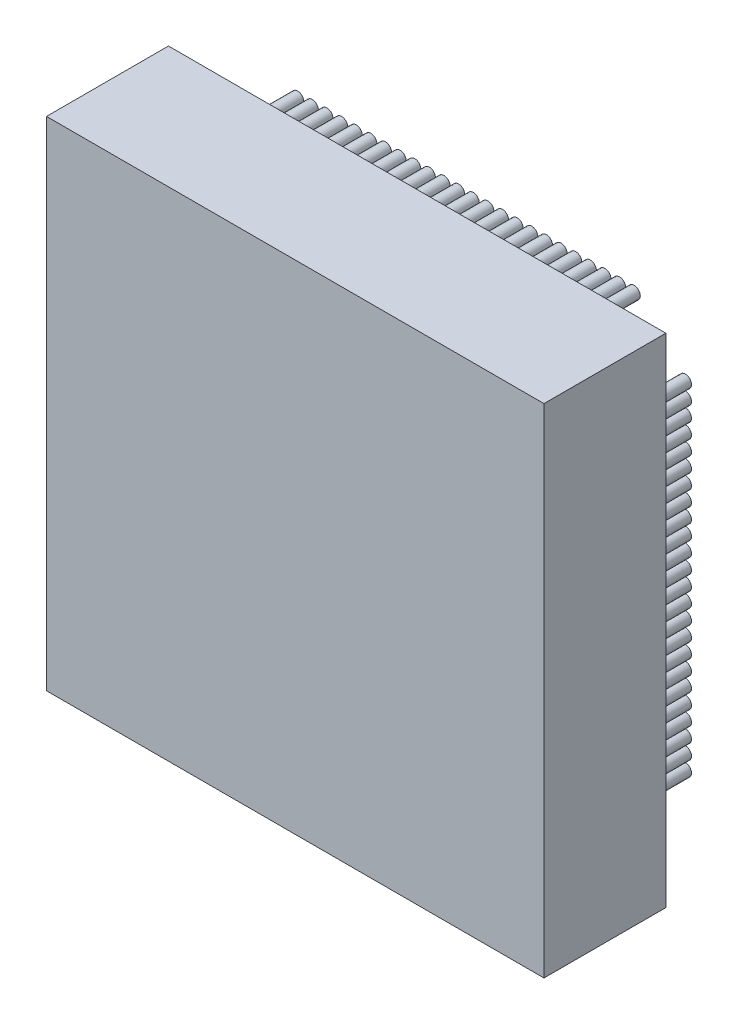
SolidWorks part; units mm, degrees
ref_plane "Front Plane" through (0, 0, 0) normal (0, 0, 1) x (1, 0, 0)
ref_plane "Top Plane" through (0, 0, 0) normal (0, 1, 0) x (1, 0, 0)
ref_plane "Right Plane" through (0, 0, 0) normal (1, 0, 0) x (0, 0, -1)
sketch "Sketch1" plane through (0, 0, 0) normal (0, 0, 1) x (1, 0, 0)
  line L0 (10.2, -10.2) -> (10.2, 10.2)
  line L1 (10.2, 10.2) -> (-10.2, 10.2)
  line L2 (-10.2, 10.2) -> (-10.2, -10.2)
  line L3 (-10.2, -10.2) -> (10.2, -10.2)
extrude "Component_Outline" add sketch "Sketch1" along normal blind 5 separate body
sketch "Sketch2" plane through (0, 0, 0) normal (0, 0, 1) x (1, 0, 0)
  circle A0 centre (-6.9, -9) radius 0.25
extrude "1" add sketch "Sketch2" against normal blind 2 separate body
sketch "Sketch3" plane through (0, 0, 0) normal (0, 0, 1) x (1, 0, 0)
  circle A0 centre (-6.3, -9) radius 0.25
extrude "2" add sketch "Sketch3" against normal blind 2 separate body
sketch "Sketch4" plane through (0, 0, 0) normal (0, 0, 1) x (1, 0, 0)
  circle A0 centre (-5.7, -9) radius 0.25
extrude "3" add sketch "Sketch4" against normal blind 2 separate body
sketch "Sketch5" plane through (0, 0, 0) normal (0, 0, 1) x (1, 0, 0)
  circle A0 centre (-5.1, -9) radius 0.25
extrude "4" add sketch "Sketch5" against normal blind 2 separate body
sketch "Sketch6" plane through (0, 0, 0) normal (0, 0, 1) x (1, 0, 0)
  circle A0 centre (-4.5, -9) radius 0.25
extrude "5" add sketch "Sketch6" against normal blind 2 separate body
sketch "Sketch7" plane through (0, 0, 0) normal (0, 0, 1) x (1, 0, 0)
  circle A0 centre (-3.9, -9) radius 0.25
extrude "6" add sketch "Sketch7" against normal blind 2 separate body
sketch "Sketch8" plane through (0, 0, 0) normal (0, 0, 1) x (1, 0, 0)
  circle A0 centre (-3.3, -9) radius 0.25
extrude "7" add sketch "Sketch8" against normal blind 2 separate body
sketch "Sketch9" plane through (0, 0, 0) normal (0, 0, 1) x (1, 0, 0)
  circle A0 centre (-2.7, -9) radius 0.25
extrude "8" add sketch "Sketch9" against normal blind 2 separate body
sketch "Sketch10" plane through (0, 0, 0) normal (0, 0, 1) x (1, 0, 0)
  circle A0 centre (-2.1, -9) radius 0.25
extrude "9" add sketch "Sketch10" against normal blind 2 separate body
sketch "Sketch11" plane through (0, 0, 0) normal (0, 0, 1) x (1, 0, 0)
  circle A0 centre (-1.5, -9) radius 0.25
extrude "10" add sketch "Sketch11" against normal blind 2 separate body
sketch "Sketch12" plane through (0, 0, 0) normal (0, 0, 1) x (1, 0, 0)
  circle A0 centre (-0.9, -9) radius 0.25
extrude "11" add sketch "Sketch12" against normal blind 2 separate body
sketch "Sketch13" plane through (0, 0, 0) normal (0, 0, 1) x (1, 0, 0)
  circle A0 centre (-0.3, -9) radius 0.25
extrude "12" add sketch "Sketch13" against normal blind 2 separate body
sketch "Sketch14" plane through (0, 0, 0) normal (0, 0, 1) x (1, 0, 0)
  circle A0 centre (0.3, -9) radius 0.25
extrude "13" add sketch "Sketch14" against normal blind 2 separate body
sketch "Sketch15" plane through (0, 0, 0) normal (0, 0, 1) x (1, 0, 0)
  circle A0 centre (0.9, -9) radius 0.25
extrude "14" add sketch "Sketch15" against normal blind 2 separate body
sketch "Sketch16" plane through (0, 0, 0) normal (0, 0, 1) x (1, 0, 0)
  circle A0 centre (1.5, -9) radius 0.25
extrude "15" add sketch "Sketch16" against normal blind 2 separate body
sketch "Sketch17" plane through (0, 0, 0) normal (0, 0, 1) x (1, 0, 0)
  circle A0 centre (2.1, -9) radius 0.25
extrude "16" add sketch "Sketch17" against normal blind 2 separate body
sketch "Sketch18" plane through (0, 0, 0) normal (0, 0, 1) x (1, 0, 0)
  circle A0 centre (2.7, -9) radius 0.25
extrude "17" add sketch "Sketch18" against normal blind 2 separate body
sketch "Sketch19" plane through (0, 0, 0) normal (0, 0, 1) x (1, 0, 0)
  circle A0 centre (3.3, -9) radius 0.25
extrude "18" add sketch "Sketch19" against normal blind 2 separate body
sketch "Sketch20" plane through (0, 0, 0) normal (0, 0, 1) x (1, 0, 0)
  circle A0 centre (3.9, -9) radius 0.25
extrude "19" add sketch "Sketch20" against normal blind 2 separate body
sketch "Sketch21" plane through (0, 0, 0) normal (0, 0, 1) x (1, 0, 0)
  circle A0 centre (4.5, -9) radius 0.25
extrude "20" add sketch "Sketch21" against normal blind 2 separate body
sketch "Sketch22" plane through (0, 0, 0) normal (0, 0, 1) x (1, 0, 0)
  circle A0 centre (5.1, -9) radius 0.25
extrude "21" add sketch "Sketch22" against normal blind 2 separate body
sketch "Sketch23" plane through (0, 0, 0) normal (0, 0, 1) x (1, 0, 0)
  circle A0 centre (5.7, -9) radius 0.25
extrude "22" add sketch "Sketch23" against normal blind 2 separate body
sketch "Sketch24" plane through (0, 0, 0) normal (0, 0, 1) x (1, 0, 0)
  circle A0 centre (6.3, -9) radius 0.25
extrude "23" add sketch "Sketch24" against normal blind 2 separate body
sketch "Sketch25" plane through (0, 0, 0) normal (0, 0, 1) x (1, 0, 0)
  circle A0 centre (6.9, -9) radius 0.25
extrude "24" add sketch "Sketch25" against normal blind 2 separate body
sketch "Sketch26" plane through (0, 0, 0) normal (0, 0, 1) x (1, 0, 0)
  circle A0 centre (9, -6.9) radius 0.25
extrude "25" add sketch "Sketch26" against normal blind 2 separate body
sketch "Sketch27" plane through (0, 0, 0) normal (0, 0, 1) x (1, 0, 0)
  circle A0 centre (9, -6.3) radius 0.25
extrude "26" add sketch "Sketch27" against normal blind 2 separate body
sketch "Sketch28" plane through (0, 0, 0) normal (0, 0, 1) x (1, 0, 0)
  circle A0 centre (9, -5.7) radius 0.25
extrude "27" add sketch "Sketch28" against normal blind 2 separate body
sketch "Sketch29" plane through (0, 0, 0) normal (0, 0, 1) x (1, 0, 0)
  circle A0 centre (9, -5.1) radius 0.25
extrude "28" add sketch "Sketch29" against normal blind 2 separate body
sketch "Sketch30" plane through (0, 0, 0) normal (0, 0, 1) x (1, 0, 0)
  circle A0 centre (9, -4.5) radius 0.25
extrude "29" add sketch "Sketch30" against normal blind 2 separate body
sketch "Sketch31" plane through (0, 0, 0) normal (0, 0, 1) x (1, 0, 0)
  circle A0 centre (9, -3.9) radius 0.25
extrude "30" add sketch "Sketch31" against normal blind 2 separate body
sketch "Sketch32" plane through (0, 0, 0) normal (0, 0, 1) x (1, 0, 0)
  circle A0 centre (9, -3.3) radius 0.25
extrude "31" add sketch "Sketch32" against normal blind 2 separate body
sketch "Sketch33" plane through (0, 0, 0) normal (0, 0, 1) x (1, 0, 0)
  circle A0 centre (9, -2.7) radius 0.25
extrude "32" add sketch "Sketch33" against normal blind 2 separate body
sketch "Sketch34" plane through (0, 0, 0) normal (0, 0, 1) x (1, 0, 0)
  circle A0 centre (9, -2.1) radius 0.25
extrude "33" add sketch "Sketch34" against normal blind 2 separate body
sketch "Sketch35" plane through (0, 0, 0) normal (0, 0, 1) x (1, 0, 0)
  circle A0 centre (9, -1.5) radius 0.25
extrude "34" add sketch "Sketch35" against normal blind 2 separate body
sketch "Sketch36" plane through (0, 0, 0) normal (0, 0, 1) x (1, 0, 0)
  circle A0 centre (9, -0.9) radius 0.25
extrude "35" add sketch "Sketch36" against normal blind 2 separate body
sketch "Sketch37" plane through (0, 0, 0) normal (0, 0, 1) x (1, 0, 0)
  circle A0 centre (9, -0.3) radius 0.25
extrude "36" add sketch "Sketch37" against normal blind 2 separate body
sketch "Sketch38" plane through (0, 0, 0) normal (0, 0, 1) x (1, 0, 0)
  circle A0 centre (9, 0.3) radius 0.25
extrude "37" add sketch "Sketch38" against normal blind 2 separate body
sketch "Sketch39" plane through (0, 0, 0) normal (0, 0, 1) x (1, 0, 0)
  circle A0 centre (9, 0.9) radius 0.25
extrude "38" add sketch "Sketch39" against normal blind 2 separate body
sketch "Sketch40" plane through (0, 0, 0) normal (0, 0, 1) x (1, 0, 0)
  circle A0 centre (9, 1.5) radius 0.25
extrude "39" add sketch "Sketch40" against normal blind 2 separate body
sketch "Sketch41" plane through (0, 0, 0) normal (0, 0, 1) x (1, 0, 0)
  circle A0 centre (9, 2.1) radius 0.25
extrude "40" add sketch "Sketch41" against normal blind 2 separate body
sketch "Sketch42" plane through (0, 0, 0) normal (0, 0, 1) x (1, 0, 0)
  circle A0 centre (9, 2.7) radius 0.25
extrude "41" add sketch "Sketch42" against normal blind 2 separate body
sketch "Sketch43" plane through (0, 0, 0) normal (0, 0, 1) x (1, 0, 0)
  circle A0 centre (9, 3.3) radius 0.25
extrude "42" add sketch "Sketch43" against normal blind 2 separate body
sketch "Sketch44" plane through (0, 0, 0) normal (0, 0, 1) x (1, 0, 0)
  circle A0 centre (9, 3.9) radius 0.25
extrude "43" add sketch "Sketch44" against normal blind 2 separate body
sketch "Sketch45" plane through (0, 0, 0) normal (0, 0, 1) x (1, 0, 0)
  circle A0 centre (9, 4.5) radius 0.25
extrude "44" add sketch "Sketch45" against normal blind 2 separate body
sketch "Sketch46" plane through (0, 0, 0) normal (0, 0, 1) x (1, 0, 0)
  circle A0 centre (9, 5.1) radius 0.25
extrude "45" add sketch "Sketch46" against normal blind 2 separate body
sketch "Sketch47" plane through (0, 0, 0) normal (0, 0, 1) x (1, 0, 0)
  circle A0 centre (9, 5.7) radius 0.25
extrude "46" add sketch "Sketch47" against normal blind 2 separate body
sketch "Sketch48" plane through (0, 0, 0) normal (0, 0, 1) x (1, 0, 0)
  circle A0 centre (9, 6.3) radius 0.25
extrude "47" add sketch "Sketch48" against normal blind 2 separate body
sketch "Sketch49" plane through (0, 0, 0) normal (0, 0, 1) x (1, 0, 0)
  circle A0 centre (9, 6.9) radius 0.25
extrude "48" add sketch "Sketch49" against normal blind 2 separate body
sketch "Sketch50" plane through (0, 0, 0) normal (0, 0, 1) x (1, 0, 0)
  circle A0 centre (6.9, 9) radius 0.25
extrude "49" add sketch "Sketch50" against normal blind 2 separate body
sketch "Sketch51" plane through (0, 0, 0) normal (0, 0, 1) x (1, 0, 0)
  circle A0 centre (6.3, 9) radius 0.25
extrude "50" add sketch "Sketch51" against normal blind 2 separate body
sketch "Sketch52" plane through (0, 0, 0) normal (0, 0, 1) x (1, 0, 0)
  circle A0 centre (5.7, 9) radius 0.25
extrude "51" add sketch "Sketch52" against normal blind 2 separate body
sketch "Sketch53" plane through (0, 0, 0) normal (0, 0, 1) x (1, 0, 0)
  circle A0 centre (5.1, 9) radius 0.25
extrude "52" add sketch "Sketch53" against normal blind 2 separate body
sketch "Sketch54" plane through (0, 0, 0) normal (0, 0, 1) x (1, 0, 0)
  circle A0 centre (4.5, 9) radius 0.25
extrude "53" add sketch "Sketch54" against normal blind 2 separate body
sketch "Sketch55" plane through (0, 0, 0) normal (0, 0, 1) x (1, 0, 0)
  circle A0 centre (3.9, 9) radius 0.25
extrude "54" add sketch "Sketch55" against normal blind 2 separate body
sketch "Sketch56" plane through (0, 0, 0) normal (0, 0, 1) x (1, 0, 0)
  circle A0 centre (3.3, 9) radius 0.25
extrude "55" add sketch "Sketch56" against normal blind 2 separate body
sketch "Sketch57" plane through (0, 0, 0) normal (0, 0, 1) x (1, 0, 0)
  circle A0 centre (2.7, 9) radius 0.25
extrude "56" add sketch "Sketch57" against normal blind 2 separate body
sketch "Sketch58" plane through (0, 0, 0) normal (0, 0, 1) x (1, 0, 0)
  circle A0 centre (2.1, 9) radius 0.25
extrude "57" add sketch "Sketch58" against normal blind 2 separate body
sketch "Sketch59" plane through (0, 0, 0) normal (0, 0, 1) x (1, 0, 0)
  circle A0 centre (1.5, 9) radius 0.25
extrude "58" add sketch "Sketch59" against normal blind 2 separate body
sketch "Sketch60" plane through (0, 0, 0) normal (0, 0, 1) x (1, 0, 0)
  circle A0 centre (0.9, 9) radius 0.25
extrude "59" add sketch "Sketch60" against normal blind 2 separate body
sketch "Sketch61" plane through (0, 0, 0) normal (0, 0, 1) x (1, 0, 0)
  circle A0 centre (0.3, 9) radius 0.25
extrude "60" add sketch "Sketch61" against normal blind 2 separate body
sketch "Sketch62" plane through (0, 0, 0) normal (0, 0, 1) x (1, 0, 0)
  circle A0 centre (-0.3, 9) radius 0.25
extrude "61" add sketch "Sketch62" against normal blind 2 separate body
sketch "Sketch63" plane through (0, 0, 0) normal (0, 0, 1) x (1, 0, 0)
  circle A0 centre (-0.9, 9) radius 0.25
extrude "62" add sketch "Sketch63" against normal blind 2 separate body
sketch "Sketch64" plane through (0, 0, 0) normal (0, 0, 1) x (1, 0, 0)
  circle A0 centre (-1.5, 9) radius 0.25
extrude "63" add sketch "Sketch64" against normal blind 2 separate body
sketch "Sketch65" plane through (0, 0, 0) normal (0, 0, 1) x (1, 0, 0)
  circle A0 centre (-2.1, 9) radius 0.25
extrude "64" add sketch "Sketch65" against normal blind 2 separate body
sketch "Sketch66" plane through (0, 0, 0) normal (0, 0, 1) x (1, 0, 0)
  circle A0 centre (-2.7, 9) radius 0.25
extrude "65" add sketch "Sketch66" against normal blind 2 separate body
sketch "Sketch67" plane through (0, 0, 0) normal (0, 0, 1) x (1, 0, 0)
  circle A0 centre (-3.3, 9) radius 0.25
extrude "66" add sketch "Sketch67" against normal blind 2 separate body
sketch "Sketch68" plane through (0, 0, 0) normal (0, 0, 1) x (1, 0, 0)
  circle A0 centre (-3.9, 9) radius 0.25
extrude "67" add sketch "Sketch68" against normal blind 2 separate body
sketch "Sketch69" plane through (0, 0, 0) normal (0, 0, 1) x (1, 0, 0)
  circle A0 centre (-4.5, 9) radius 0.25
extrude "68" add sketch "Sketch69" against normal blind 2 separate body
sketch "Sketch70" plane through (0, 0, 0) normal (0, 0, 1) x (1, 0, 0)
  circle A0 centre (-5.1, 9) radius 0.25
extrude "69" add sketch "Sketch70" against normal blind 2 separate body
sketch "Sketch71" plane through (0, 0, 0) normal (0, 0, 1) x (1, 0, 0)
  circle A0 centre (-5.7, 9) radius 0.25
extrude "70" add sketch "Sketch71" against normal blind 2 separate body
sketch "Sketch72" plane through (0, 0, 0) normal (0, 0, 1) x (1, 0, 0)
  circle A0 centre (-6.3, 9) radius 0.25
extrude "71" add sketch "Sketch72" against normal blind 2 separate body
sketch "Sketch73" plane through (0, 0, 0) normal (0, 0, 1) x (1, 0, 0)
  circle A0 centre (-6.9, 9) radius 0.25
extrude "72" add sketch "Sketch73" against normal blind 2 separate body
sketch "Sketch74" plane through (0, 0, 0) normal (0, 0, 1) x (1, 0, 0)
  circle A0 centre (-9, 6.9) radius 0.25
extrude "73" add sketch "Sketch74" against normal blind 2 separate body
sketch "Sketch75" plane through (0, 0, 0) normal (0, 0, 1) x (1, 0, 0)
  circle A0 centre (-9, 6.3) radius 0.25
extrude "74" add sketch "Sketch75" against normal blind 2 separate body
sketch "Sketch76" plane through (0, 0, 0) normal (0, 0, 1) x (1, 0, 0)
  circle A0 centre (-9, 5.7) radius 0.25
extrude "75" add sketch "Sketch76" against normal blind 2 separate body
sketch "Sketch77" plane through (0, 0, 0) normal (0, 0, 1) x (1, 0, 0)
  circle A0 centre (-9, 5.1) radius 0.25
extrude "76" add sketch "Sketch77" against normal blind 2 separate body
sketch "Sketch78" plane through (0, 0, 0) normal (0, 0, 1) x (1, 0, 0)
  circle A0 centre (-9, 4.5) radius 0.25
extrude "77" add sketch "Sketch78" against normal blind 2 separate body
sketch "Sketch79" plane through (0, 0, 0) normal (0, 0, 1) x (1, 0, 0)
  circle A0 centre (-9, 3.9) radius 0.25
extrude "78" add sketch "Sketch79" against normal blind 2 separate body
sketch "Sketch80" plane through (0, 0, 0) normal (0, 0, 1) x (1, 0, 0)
  circle A0 centre (-9, 3.3) radius 0.25
extrude "79" add sketch "Sketch80" against normal blind 2 separate body
sketch "Sketch81" plane through (0, 0, 0) normal (0, 0, 1) x (1, 0, 0)
  circle A0 centre (-9, 2.7) radius 0.25
extrude "80" add sketch "Sketch81" against normal blind 2 separate body
sketch "Sketch82" plane through (0, 0, 0) normal (0, 0, 1) x (1, 0, 0)
  circle A0 centre (-9, 2.1) radius 0.25
extrude "81" add sketch "Sketch82" against normal blind 2 separate body
sketch "Sketch83" plane through (0, 0, 0) normal (0, 0, 1) x (1, 0, 0)
  circle A0 centre (-9, 1.5) radius 0.25
extrude "82" add sketch "Sketch83" against normal blind 2 separate body
sketch "Sketch84" plane through (0, 0, 0) normal (0, 0, 1) x (1, 0, 0)
  circle A0 centre (-9, 0.9) radius 0.25
extrude "83" add sketch "Sketch84" against normal blind 2 separate body
sketch "Sketch85" plane through (0, 0, 0) normal (0, 0, 1) x (1, 0, 0)
  circle A0 centre (-9, 0.3) radius 0.25
extrude "84" add sketch "Sketch85" against normal blind 2 separate body
sketch "Sketch86" plane through (0, 0, 0) normal (0, 0, 1) x (1, 0, 0)
  circle A0 centre (-9, -0.3) radius 0.25
extrude "85" add sketch "Sketch86" against normal blind 2 separate body
sketch "Sketch87" plane through (0, 0, 0) normal (0, 0, 1) x (1, 0, 0)
  circle A0 centre (-9, -0.9) radius 0.25
extrude "86" add sketch "Sketch87" against normal blind 2 separate body
sketch "Sketch88" plane through (0, 0, 0) normal (0, 0, 1) x (1, 0, 0)
  circle A0 centre (-9, -1.5) radius 0.25
extrude "87" add sketch "Sketch88" against normal blind 2 separate body
sketch "Sketch89" plane through (0, 0, 0) normal (0, 0, 1) x (1, 0, 0)
  circle A0 centre (-9, -2.1) radius 0.25
extrude "88" add sketch "Sketch89" against normal blind 2 separate body
sketch "Sketch90" plane through (0, 0, 0) normal (0, 0, 1) x (1, 0, 0)
  circle A0 centre (-9, -2.7) radius 0.25
extrude "89" add sketch "Sketch90" against normal blind 2 separate body
sketch "Sketch91" plane through (0, 0, 0) normal (0, 0, 1) x (1, 0, 0)
  circle A0 centre (-9, -3.3) radius 0.25
extrude "90" add sketch "Sketch91" against normal blind 2 separate body
sketch "Sketch92" plane through (0, 0, 0) normal (0, 0, 1) x (1, 0, 0)
  circle A0 centre (-9, -3.9) radius 0.25
extrude "91" add sketch "Sketch92" against normal blind 2 separate body
sketch "Sketch93" plane through (0, 0, 0) normal (0, 0, 1) x (1, 0, 0)
  circle A0 centre (-9, -4.5) radius 0.25
extrude "92" add sketch "Sketch93" against normal blind 2 separate body
sketch "Sketch94" plane through (0, 0, 0) normal (0, 0, 1) x (1, 0, 0)
  circle A0 centre (-9, -5.1) radius 0.25
extrude "93" add sketch "Sketch94" against normal blind 2 separate body
sketch "Sketch95" plane through (0, 0, 0) normal (0, 0, 1) x (1, 0, 0)
  circle A0 centre (-9, -5.7) radius 0.25
extrude "94" add sketch "Sketch95" against normal blind 2 separate body
sketch "Sketch96" plane through (0, 0, 0) normal (0, 0, 1) x (1, 0, 0)
  circle A0 centre (-9, -6.3) radius 0.25
extrude "95" add sketch "Sketch96" against normal blind 2 separate body
sketch "Sketch97" plane through (0, 0, 0) normal (0, 0, 1) x (1, 0, 0)
  circle A0 centre (-9, -6.9) radius 0.25
extrude "96" add sketch "Sketch97" against normal blind 2 separate body
sketch3d "3DSketch1"
  line L0 (0, 0, 0) -> (1, 0, 0)
  line L1 (0, 0, 0) -> (0, 1, 0)
  line L2 (0, 0, 0) -> (0, 0, 1)
  point P0 (0, 0, 0)
